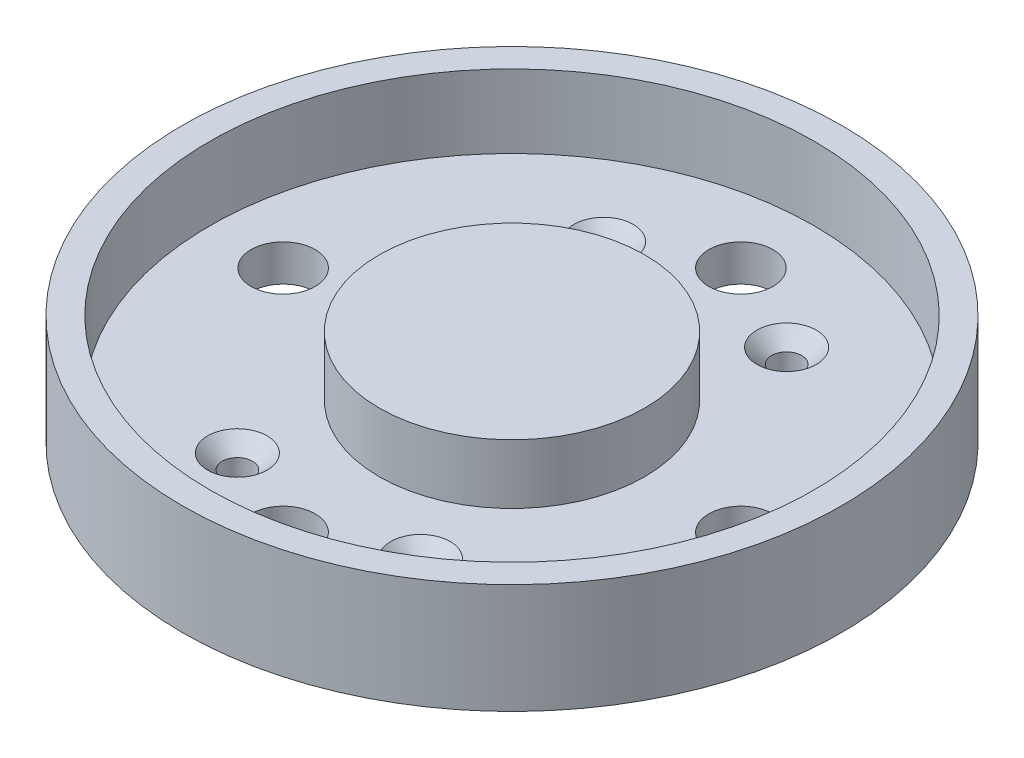
SolidWorks part; units mm, degrees
ref_plane "Front Plane" through (0, 0, 0) normal (0, 0, 1) x (1, 0, 0)
ref_plane "Top Plane" through (0, 0, 0) normal (0, 1, 0) x (1, 0, 0)
ref_plane "Right Plane" through (0, 0, 0) normal (1, 0, 0) x (0, 0, -1)
sketch "Sketch1" plane through (0, 0, 0) normal (0, 1, 0) x (1, 0, 0)
  line L0 (0, 0) -> (0, 36) construction
  line L1 (0, 0) -> (-36, 0) construction
  circle A0 centre (0, 0) radius 36
  circle A5 centre (25, 0) radius 3.5
  circle A6 centre (0, -25) radius 3.5
  circle A7 centre (-10, 20) radius 1.65
  circle A8 centre (10, 20) radius 1.65
  circle A9 centre (10, -20) radius 1.65
  circle A10 centre (-10, -20) radius 1.65
  circle A11 centre (0, 25) radius 3.5
  circle A13 centre (-25, 0) radius 3.5
  point P14 (0, 0)
  point P25 (0, 0)
  dimension "D1" = 25
  dimension "D2" = 7
  dimension "D4" = 72
  dimension "D5" = 3.3
  dimension "D6" = 20
  dimension "D7" = 10
  dimension "D3" = 4
extrude "Boss-Extrude1" add sketch "Sketch1" along normal blind 4
sketch "Sketch2" plane through (0, 4, 0) normal (0, 1, 0) x (1, 0, 0)
  circle A0 centre (0, 0) radius 14.5
  dimension "D1" = 29
extrude "Boss-Extrude2" add sketch "Sketch2" along normal blind 6.5
sketch "Sketch3" plane through (0, 4, 0) normal (0, 1, 0) x (1, 0, 0)
  circle A0 centre (0, 0) radius 33
  circle A1 centre (0, 0) radius 36 construction
  circle A2 centre (0, 0) radius 36
  dimension "D1" = 66
extrude "Boss-Extrude3" add sketch "Sketch3" along normal blind 8
chamfer "Chamfer1" distance 1.6 angle 45 4 edges at (-10, 4, 18.35) (10, 4, 21.65) (10, 4, -21.65) (-10, 4, -18.35)
